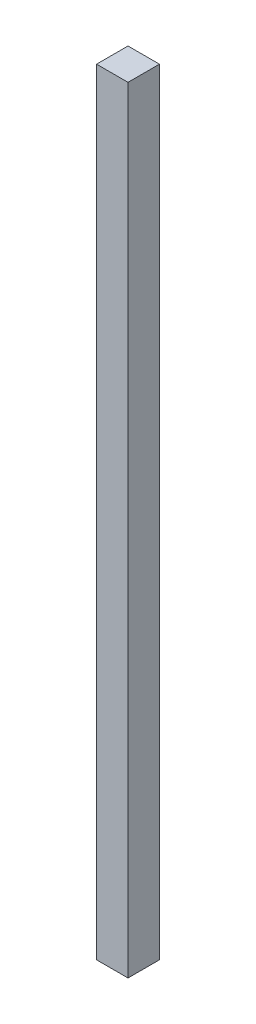
SolidWorks part; units mm, degrees
ref_plane "Front Plane" through (0, 0, 0) normal (0, 0, 1) x (1, 0, 0)
ref_plane "Top Plane" through (0, 0, 0) normal (0, 1, 0) x (1, 0, 0)
ref_plane "Right Plane" through (0, 0, 0) normal (1, 0, 0) x (0, 0, -1)
sketch "Sketch1" plane through (0, 0, 0) normal (0, 1, 0) x (1, 0, 0)
  line L1 (7.5, 7.5) -> (-7.5, 7.5)
  line L2 (7.5, 7.5) -> (7.5, -7.5)
  line L3 (7.5, -7.5) -> (-7.5, -7.5)
  line L4 (-7.5, 7.5) -> (-7.5, -7.5)
  line L5 (7.5, 7.5) -> (-7.5, -7.5) construction
  line L6 (7.5, -7.5) -> (-7.5, 7.5) construction
  point P0 (0, 0)
  dimension "D1" = 15
  dimension "D2" = 15
extrude "Boss-Extrude1" add sketch "Sketch1" along normal blind 370
